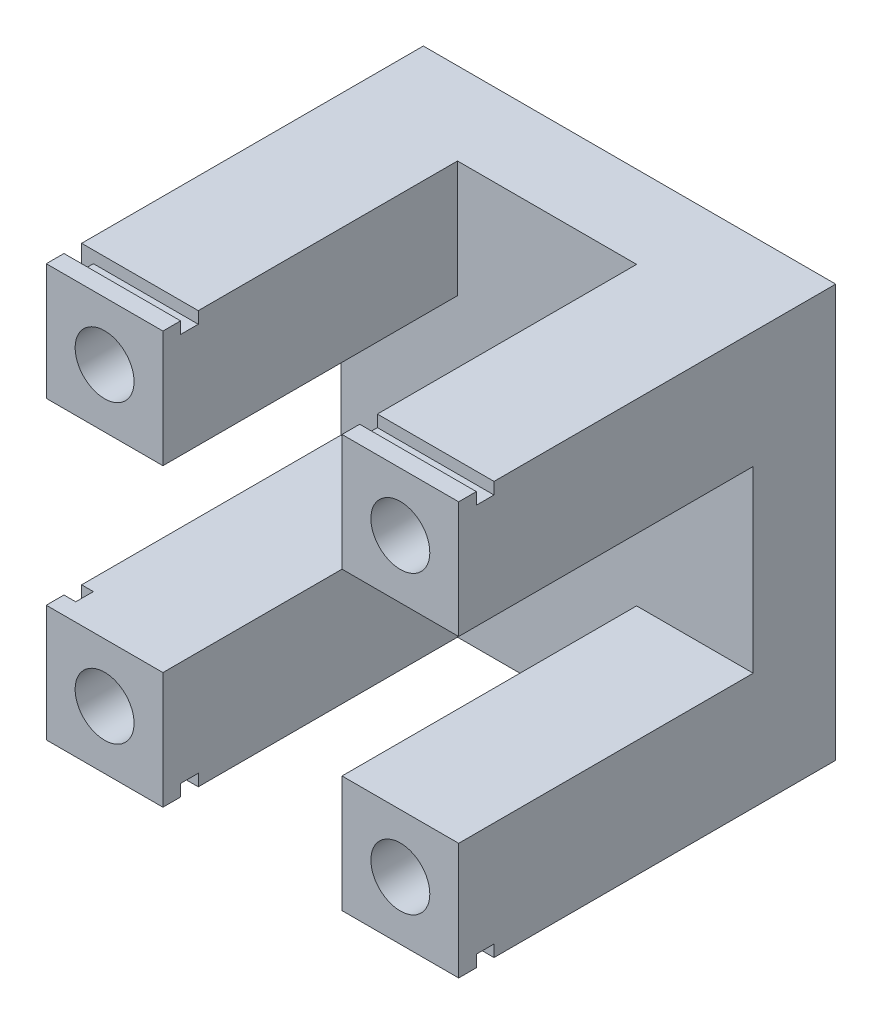
SolidWorks part; units mm, degrees
ref_plane "Plan de face" through (0, 0, 0) normal (0, 0, 1) x (1, 0, 0)
ref_plane "Plan de dessus" through (0, 0, 0) normal (0, 1, 0) x (1, 0, 0)
ref_plane "Plan de droite" through (0, 0, 0) normal (1, 0, 0) x (0, 0, -1)
sketch "Esquisse1" plane through (0, 0, 0) normal (0, 0, 1) x (1, 0, 0)
  line L1 (0, 0) -> (-70, 0)
  line L2 (0, 0) -> (0, 70)
  line L3 (0, 70) -> (-70, 70)
  line L4 (-70, 0) -> (-70, 70)
  dimension "D1" = 70
  dimension "D2" = 70
extrude "Boss.-Extru.1" add sketch "Esquisse1" along normal blind 64
sketch "Esquisse2" plane through (0, 0, 64) normal (0, 0, 1) x (1, 0, 0)
  line L0 (-70, 70) -> (-70, 0) construction
  line L1 (-70, 50.2) -> (0, 50.2)
  line L2 (-70, 50.2) -> (-70, 19.8)
  line L3 (-70, 19.8) -> (0, 19.8)
  line L4 (0, 50.2) -> (0, 19.8)
  line L5 (0, 0) -> (0, 70) construction
  line L6 (-70, 0) -> (0, 0) construction
  line L7 (-19.8, 0) -> (-50.2, 0)
  line L8 (-19.8, 0) -> (-19.8, 70)
  line L9 (-19.8, 70) -> (-50.2, 70)
  line L10 (-50.2, 0) -> (-50.2, 70)
  line L11 (0, 70) -> (-70, 70) construction
  line M5 (0, 0) -> (0, 70)
  line M6 (0, 70) -> (-70, 70)
  line M7 (-70, 70) -> (-70, 0)
  line M8 (-70, 0) -> (0, 0)
  dimension "D1" = 30.4
  dimension "D2" = 19.8
  dimension "D3" = 30.4
  dimension "D4" = 19.8
extrude "Enlèv. mat.-Extru.1" cut sketch "Esquisse2" against normal blind 50 contours L10 L1 L8 M6 | L10 L3 L8 L1 | L8 L3 L1 M5 | L3 L10 L1 M7 | L10 L8 L3 M8
sketch "Esquisse5" plane through (-70, 0, 0) normal (-1, 0, 0) x (0, 0, 1)
  line L0 (64, 70) -> (0, 70) construction
  line L1 (61, 70) -> (58, 70)
  line L2 (61, 70) -> (61, 68)
  line L3 (61, 68) -> (58, 68)
  line L4 (58, 70) -> (58, 68)
  line L5 (64, 0) -> (0, 0) construction
  line L6 (61, 0) -> (58, 0)
  line L7 (61, 0) -> (61, 2)
  line L8 (61, 2) -> (58, 2)
  line L9 (58, 0) -> (58, 2)
  line L10 (64, 19.8) -> (64, 0) construction
  line L11 (64, 70) -> (64, 50.2) construction
  dimension "D1" = 3
  dimension "D2" = 3
  dimension "D3" = 2
  dimension "D4" = 2
  dimension "D5" = 3
  dimension "D6" = 3
extrude "Enlèv. mat.-Extru.3" cut sketch "Esquisse5" against normal through all
sketch "Esquisse6" plane through (0, 70, 0) normal (0, 1, 0) x (1, 0, 0)
  line L0 (-50.2, -61) -> (-70, -61) construction
  line L1 (-70, -58) -> (-68, -58)
  line L2 (-70, -58) -> (-70, -61)
  line L3 (-70, -61) -> (-68, -61)
  line L4 (-68, -58) -> (-68, -61)
  dimension "D1" = 2
extrude "Enlèv. mat.-Extru.4" cut sketch "Esquisse6" against normal through all
sketch3d "Esquisse3D2"
  line L0 (-35, 35, 57.383) -> (-35, 35, -1.6203) construction
  point P2 (0, 35, 0)
  point P5 (0, 35, 64)
  dimension "D1" = 35
  dimension "D2" = 35
  dimension "D3" = 35
sketch "Esquisse7" plane through (0, 0, 64) normal (0, 0, 1) x (1, 0, 0)
  line L0 (-19.8, 0) -> (0, 0) construction
  line L1 (-19.8, 19.8) -> (0, 19.8) construction
  line L2 (-19.8, 0) -> (-19.8, 19.8) construction
  line L3 (0, 0) -> (0, 19.8) construction
  circle A0 centre (-9.9, 9.9) radius 5
  dimension "D1" = 10
  dimension "D2" = 9.9
  dimension "D3" = 9.9
  dimension "D4" = 9.9
  dimension "D5" = 9.9
extrude "Enlèv. mat.-Extru.5" cut sketch "Esquisse7" against normal through all
pattern_circular "Répétition circulaire2" count 4 every 90 about axis through (-35, 35, 0) along (0, 0, 1) of "Enlèv. mat.-Extru.5"
